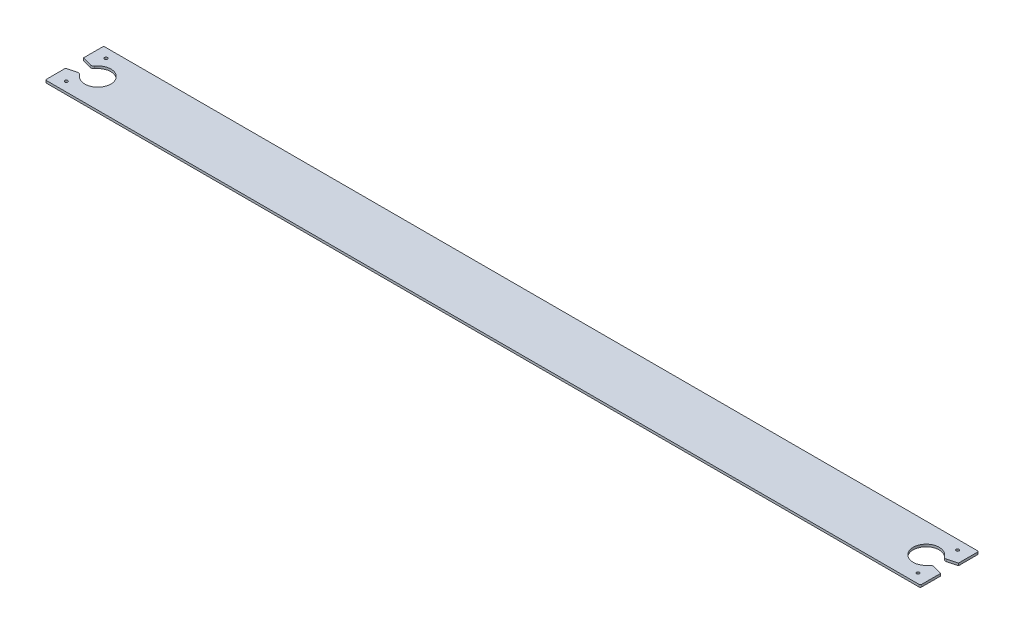
SolidWorks part; units mm, degrees
ref_plane "Front Plane" through (0, 0, 0) normal (0, 0, 1) x (1, 0, 0)
ref_plane "Top Plane" through (0, 0, 0) normal (0, 1, 0) x (1, 0, 0)
ref_plane "Right Plane" through (0, 0, 0) normal (1, 0, 0) x (0, 0, -1)
sketch "Sketch1" plane through (0, 0, 0) normal (0, 1, 0) x (1, 0, 0)
  line L0 (375, 50) -> (375, 0) construction
  line L1 (0, 0) -> (750, 0)
  line L2 (0, 0) -> (0, 50)
  line L3 (0, 50) -> (750, 50)
  line L4 (750, 0) -> (750, 50)
  circle A0 centre (10, 42) radius 1.25
  circle A1 centre (10, 8) radius 1.25
  circle A2 centre (740, 8) radius 1.25
  circle A3 centre (740, 42) radius 1.25
  dimension "D3" = 2.5
  dimension "D1" = 50
  dimension "D2" = 750
  dimension "D4" = 10
  dimension "D5" = 8
  dimension "D6" = 8
extrude "Boss-Extrude1" add sketch "Sketch1" along normal blind 2
fillet "Fillet1" radius 1 4 edges at (0, 1, 0) (0, 1, -50) (750, 1, -50) (750, 1, 0)
sketch "Sketch2" plane through (0, 2, 0) normal (0, 1, 0) x (1, 0, 0)
  line L0 (750, 25) -> (730, 25) construction
  line L1 (750, 1) -> (750, 49) construction
  line L2 (740, 25) -> (740, 30) construction
  line L3 (741.815, 30.4863) -> (750, 32.6795)
  line L4 (741.815, 19.5137) -> (750, 17.3205)
  line L5 (750, 32.6795) -> (750, 17.3205)
  line L6 (375, 50) -> (375, 0) construction
  line L7 (749, 50) -> (1, 50) construction
  line L8 (1, 0) -> (749, 0) construction
  line L9 (10, 25) -> (10, 30) construction
  line L10 (0, 25) -> (20, 25) construction
  line L11 (0, 32.6795) -> (0, 17.3205)
  line L12 (8.185, 19.5137) -> (0, 17.3205)
  line L13 (8.185, 30.4863) -> (0, 32.6795)
  arc A0 (739.1271, 31.4573) -> (739.1271, 18.5427) centre (730, 25) ccw
  arc A1 (741.815, 19.5137) -> (739.1271, 18.5427) centre (741.168, 17.0989) ccw
  arc A2 (739.1271, 31.4573) -> (741.815, 30.4863) centre (741.168, 32.9011) ccw
  arc A3 (10.8729, 31.4573) -> (8.185, 30.4863) centre (8.832, 32.9011) cw
  arc A4 (8.185, 19.5137) -> (10.8729, 18.5427) centre (8.832, 17.0989) cw
  arc A5 (10.8729, 31.4573) -> (10.8729, 18.5427) centre (20, 25) cw
  point P11 (740, 20)
  point P33 (10, 20)
  dimension "D5" = 2.5
  dimension "D1" = 20
  dimension "D2" = 5
  dimension "D3" = 10
  dimension "D4" = 15
extrude "Cut-Extrude1" cut sketch "Sketch2" against normal up to surface (2 mm away) up to face at (740, 0, -9.25)
